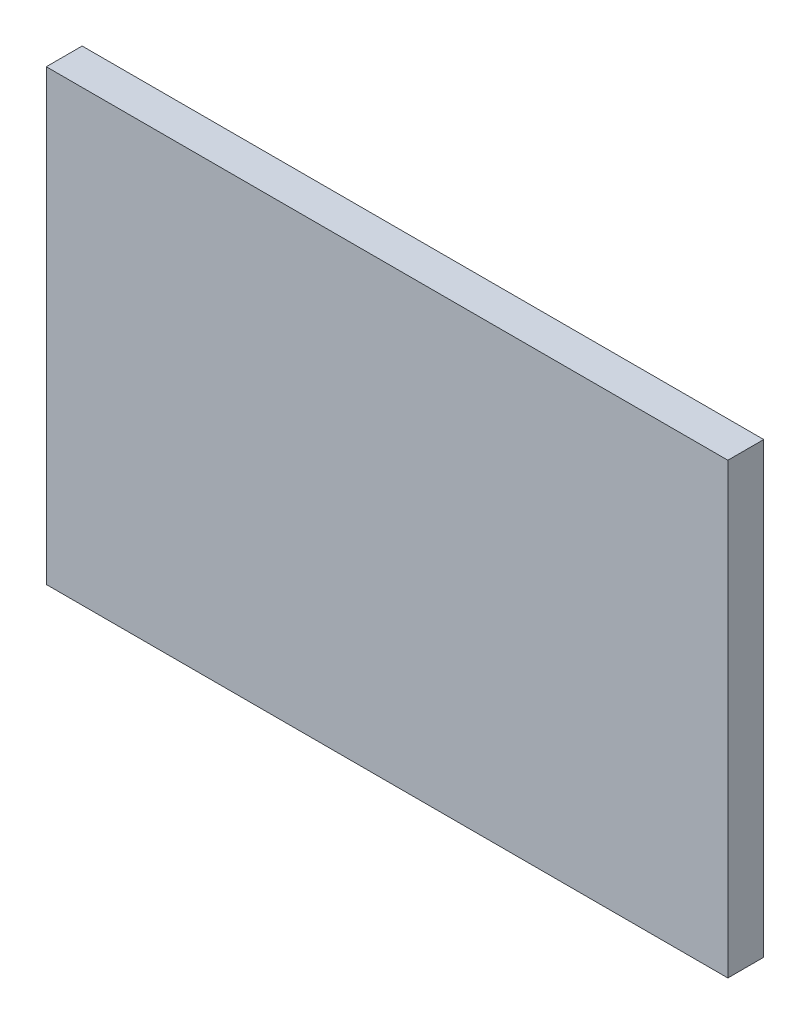
SolidWorks part; units mm, degrees
ref_plane "Ön Düzlem" through (0, 0, 0) normal (0, 0, 1) x (1, 0, 0)
ref_plane "Üst Düzlem" through (0, 0, 0) normal (0, 1, 0) x (1, 0, 0)
ref_plane "Sağ Düzlem" through (0, 0, 0) normal (1, 0, 0) x (0, 0, -1)
sketch "Çizim1" plane through (0, 0, 0) normal (0, 0, 1) x (1, 0, 0)
  line L1 (-131.588, 75.8065) -> (248.412, 75.8065)
  line L2 (-131.588, 75.8065) -> (-131.588, -174.1935)
  line L3 (-131.588, -174.1935) -> (248.412, -174.1935)
  line L4 (248.412, 75.8065) -> (248.412, -174.1935)
  dimension "D1" = 250
  dimension "D2" = 380
extrude "Yükseklik-Ekstrüzyon1" add sketch "Çizim1" along normal blind 20
